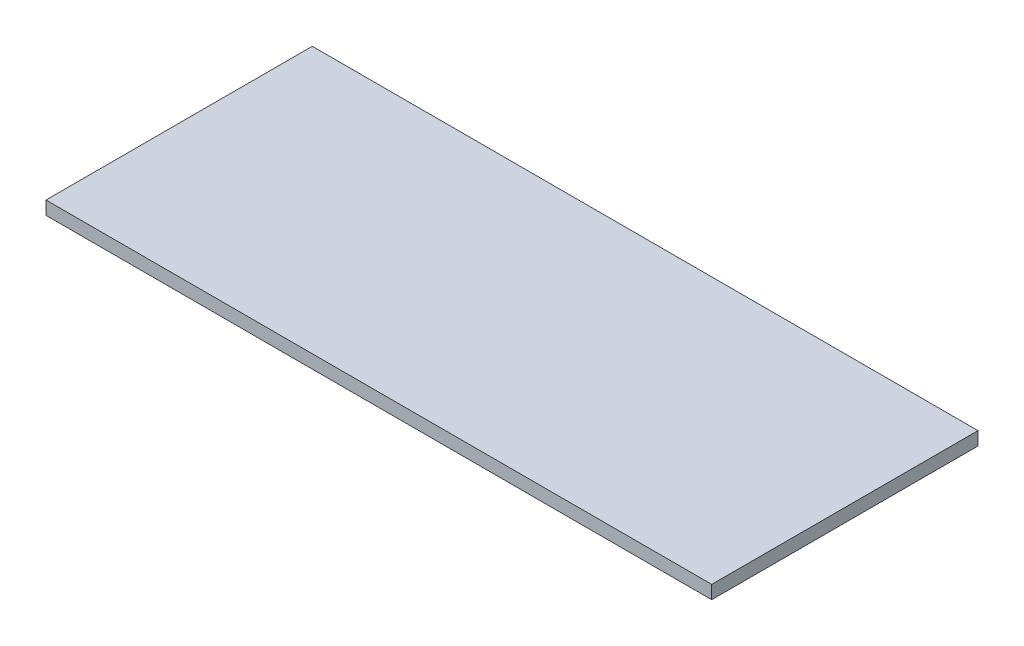
SolidWorks part; units mm, degrees
ref_plane "Front Plane" through (0, 0, 0) normal (0, 0, 1) x (1, 0, 0)
ref_plane "Top Plane" through (0, 0, 0) normal (0, 1, 0) x (1, 0, 0)
ref_plane "Right Plane" through (0, 0, 0) normal (1, 0, 0) x (0, 0, -1)
sketch "Sketch1" plane through (0, 0, 0) normal (0, 1, 0) x (1, 0, 0)
  line L0 (-750, 54.4728) -> (750, 54.4728)
  line L1 (-750, 54.4728) -> (-750, -545.5272)
  line L2 (-750, -545.5272) -> (750, -545.5272)
  line L3 (750, -545.5272) -> (750, 54.4728)
  point P3 (0, 54.4728)
  dimension "D1" = 1500
  dimension "D2" = 600
extrude "Boss-Extrude1" add sketch "Sketch1" along normal blind 30
